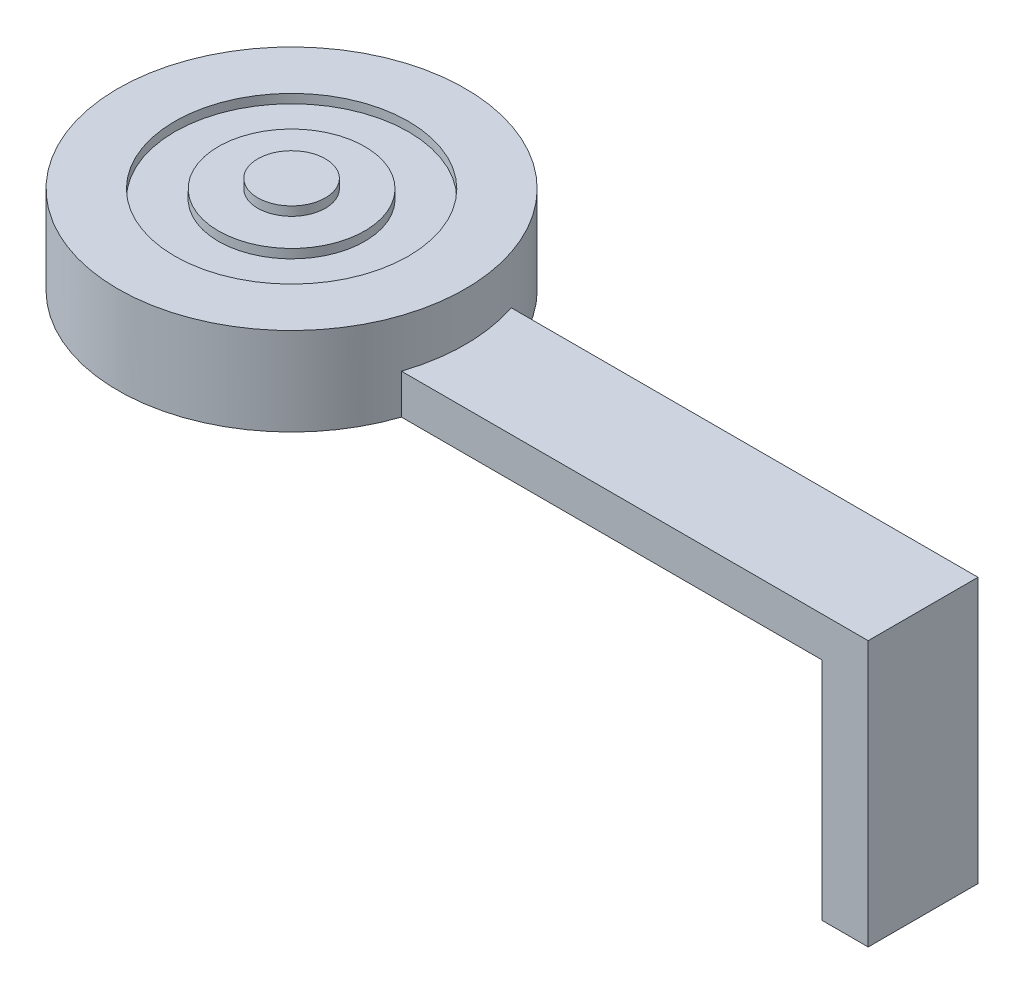
SolidWorks part; units mm, degrees
ref_plane "Front Plane" through (0, 0, 0) normal (0, 0, 1) x (1, 0, 0)
ref_plane "Top Plane" through (0, 0, 0) normal (0, 1, 0) x (1, 0, 0)
ref_plane "Right Plane" through (0, 0, 0) normal (1, 0, 0) x (0, 0, -1)
sketch "Sketch1" plane through (0, 0, 0) normal (0, 1, 0) x (1, 0, 0)
  circle A0 centre (0, 0) radius 9.779
  dimension "D1" = 19.558
extrude "Boss-Extrude1" add sketch "Sketch1" along normal blind 4.953
sketch "Sketch2" plane through (0, 4.953, 0) normal (0, 1, 0) x (1, 0, 0)
  circle A0 centre (0, 0) radius 1.905
  dimension "D1" = 3.81
extrude "Boss-Extrude2" add sketch "Sketch2" along normal blind 0.508
sketch "Sketch3" plane through (0, 4.953, 0) normal (0, 1, 0) x (1, 0, 0)
  circle A0 centre (0, 0) radius 4.1197
  circle A1 centre (0, 0) radius 6.5786
extrude "Cut-Extrude1" cut sketch "Sketch3" against normal blind 0.508
sketch "Sketch4" plane through (0, 0, 0) normal (1, 0, 0) x (0, 0, -1)
  line L0 (-9.779, 0) -> (9.779, 0) construction
  line L1 (-3.092, 2.2402) -> (3.092, 2.2402)
  line L2 (-3.092, 2.2402) -> (-3.092, 0)
  line L3 (-3.092, 0) -> (3.092, 0)
  line L4 (3.092, 2.2402) -> (3.092, 0)
  line L5 (-3.092, 2.2402) -> (3.092, 0) construction
  line L6 (-3.092, 0) -> (3.092, 2.2402) construction
  point P0 (0, 1.1201)
extrude "Boss-Extrude3" add sketch "Sketch4" along normal blind 35.56
sketch "Sketch5" plane through (0, 0, 0) normal (0, -1, 0) x (1, 0, 0)
  line L0 (35.56, -3.092) -> (9.2773, -3.092) construction
  line L1 (35.56, 3.092) -> (32.9561, 3.092)
  line L2 (35.56, 3.092) -> (35.56, -3.092)
  line L3 (35.56, -3.092) -> (32.9561, -3.092)
  line L4 (32.9561, 3.092) -> (32.9561, -3.092)
extrude "Boss-Extrude4" add sketch "Sketch5" along normal blind 12.7
